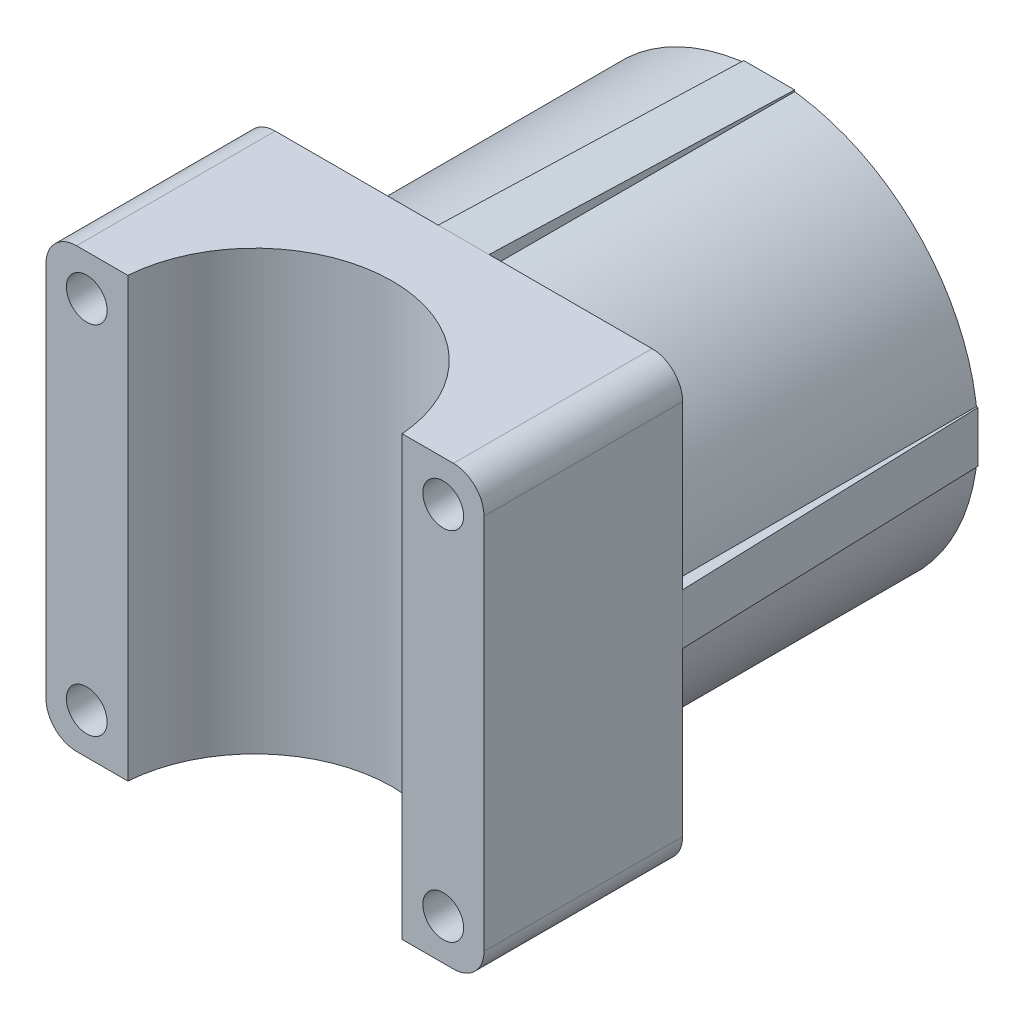
SolidWorks part; units mm, degrees
ref_plane "Alzado" through (0, 0, 0) normal (0, 0, 1) x (1, 0, 0)
ref_plane "Planta" through (0, 0, 0) normal (0, 1, 0) x (1, 0, 0)
ref_plane "Vista lateral" through (0, 0, 0) normal (1, 0, 0) x (0, 0, -1)
sketch "Croquis1" plane through (0, 0, 0) normal (0, 0, 1) x (1, 0, 0)
  line L1 (-80.0043, 43.6418) -> (-37.0043, 43.6418)
  line L2 (-80.0043, 43.6418) -> (-80.0043, 0.6418)
  line L3 (-80.0043, 0.6418) -> (-37.0043, 0.6418)
  line L4 (-37.0043, 43.6418) -> (-37.0043, 0.6418)
  dimension "D1" = 43
  dimension "D2" = 43
extrude "Saliente-Extruir1" add sketch "Croquis1" along normal blind 19.5
sketch "Croquis2" plane through (0, 43.6418, 0) normal (0, 1, 0) x (1, 0, 0)
  line L0 (-37.0043, -19.5) -> (-80.0043, -19.5) construction
  circle A0 centre (-58.5043, -20.5) radius 13.5
  point P2 (-58.5043, -19.5)
  dimension "D1" = 27
  dimension "D2" = 1
extrude "Cortar-Extruir1" cut sketch "Croquis2" against normal through all
sketch "Croquis3" plane through (0, 0, 19.5) normal (0, 0, 1) x (1, 0, 0)
  line L0 (-71.9672, 43.6418) -> (-80.0043, 43.6418) construction
  line L1 (-80.0043, 43.6418) -> (-80.0043, 0.6418) construction
  line L2 (-80.0043, 22.1418) -> (-37.0043, 22.1418) construction
  line L3 (-37.0043, 0.6418) -> (-37.0043, 43.6418) construction
  line L4 (-58.5043, 22.1418) -> (-58.5043, 11.1794) construction
  circle A0 centre (-76.0043, 39.6418) radius 2
  circle A1 centre (-41.0043, 39.6418) radius 2
  circle A2 centre (-41.0043, 4.6418) radius 2
  circle A3 centre (-76.0043, 4.6418) radius 2
  point P2 (-75.9858, 43.6418)
  dimension "D1" = 4
  dimension "D2" = 4
  dimension "D3" = 4
extrude "Cortar-Extruir2" cut sketch "Croquis3" against normal through all
fillet "Redondeo1" radius 3 4 edges at (-80.0043, 0.6418, 9.75) (-37.0043, 0.6418, 9.75) (-37.0043, 43.6418, 9.75) (-80.0043, 43.6418, 9.75)
sketch "Croquis5" plane through (0, 0, 0) normal (0, 0, -1) x (-1, 0, 0)
  circle A0 centre (58.5043, 22.1418) radius 16.5
  circle A1 centre (58.5043, 22.1418) radius 20.5
  dimension "D1" = 4
  dimension "D2" = 33
extrude "Saliente-Extruir2" add sketch "Croquis5" along normal blind 30
sketch "Croquis6" plane through (0, 0, -30) normal (0, 0, -1) x (-1, 0, 0)
  line L0 (58.5043, 42.6418) -> (58.5043, 1.6418) construction
  line L1 (38.0043, 22.1418) -> (79.0043, 22.1418) construction
  circle A0 centre (58.5043, 22.1418) radius 20.5 construction
ref_plane "Plano1" through (0, 43.5934, -1.4531) normal (0, -0.9994, 0.0333) x (-1, 0, 0)
sketch "Croquis7" plane through (0, 43.5934, -1.4531) normal (0, -0.9994, 0.0333) x (-1, 0, 0)
  line L0 (58.5043, -1.4539) -> (58.5043, 28.5627)
  line L1 (40.0043, -1.4539) -> (77.0043, -1.4539) construction
extrude "Extruir-Lámina1" add sketch "Croquis7" along normal up to next thin contours L0 thin type mid plane wall 5
ref_plane "Plano2" through (-36.9633, 0, 1.2321) normal (-0.9994, 0, 0.0333) x (0.0333, 0, 0.9994)
sketch "Croquis8" plane through (-36.9633, 0, 1.2321) normal (-0.9994, 0, 0.0333) x (0.0333, 0, 0.9994)
  line L0 (-1.2328, 22.1418) -> (-31.2495, 22.1418)
  line L1 (-1.2328, 3.6418) -> (-1.2328, 40.6418) construction
extrude "Extruir-Lámina2" add sketch "Croquis8" along normal up to next thin contours L0 thin type mid plane wall 5
ref_plane "Plano3" through (0, 0.6411, 0.0214) normal (0, 0.9994, 0.0333) x (1, 0, 0)
sketch "Croquis9" plane through (0, 0.6411, 0.0214) normal (0, 0.9994, 0.0333) x (1, 0, 0)
  line L0 (-58.5043, 30.038) -> (-58.5043, 0.0214)
  line L1 (-77.0043, 0.0214) -> (-40.0043, 0.0214) construction
extrude "Extruir-Lámina3" add sketch "Croquis9" along normal up to next thin thin type mid plane wall 5
ref_plane "Plano4" through (-79.9155, 0, -2.6639) normal (0.9994, 0, 0.0333) x (0.0333, 0, -0.9994)
sketch "Croquis10" plane through (-79.9155, 0, -2.6639) normal (0.9994, 0, 0.0333) x (0.0333, 0, -0.9994)
  line L0 (27.3513, 22.1418) -> (-2.6653, 22.1418)
  line L1 (-2.6653, 40.6418) -> (-2.6653, 3.6418) construction
extrude "Extruir-Lámina4" add sketch "Croquis10" along normal up to next thin thin type mid plane wall 5
